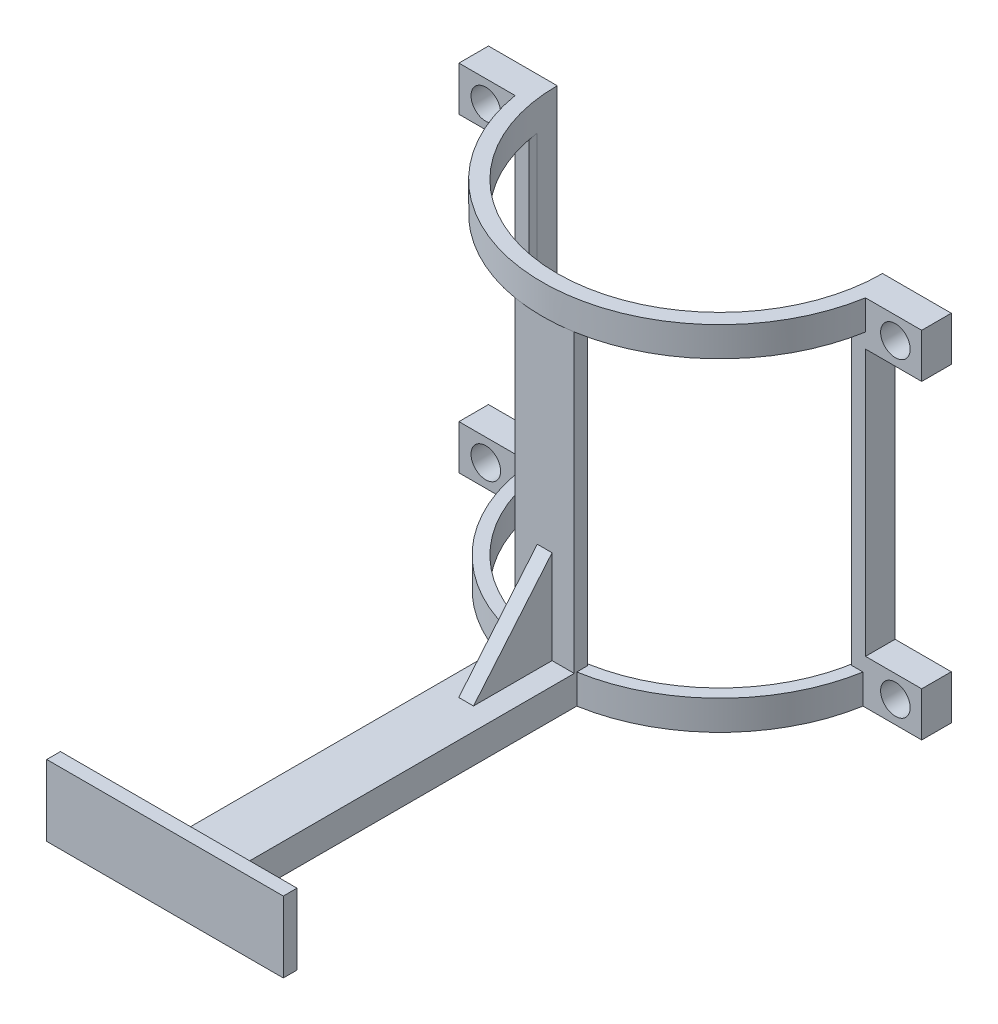
SolidWorks part; units mm, degrees
ref_plane "前视基准面" through (0, 0, 0) normal (0, 0, 1) x (1, 0, 0)
ref_plane "上视基准面" through (0, 0, 0) normal (0, 1, 0) x (1, 0, 0)
ref_plane "右视基准面" through (0, 0, 0) normal (1, 0, 0) x (0, 0, -1)
sketch "草图1" plane through (0, 0, 0) normal (0, 1, 0) x (1, 0, 0)
  line L0 (-118.5, 0) -> (-108.5, 0)
  line L1 (108.5, 0) -> (118.5, 0)
  arc A1 (-118.5, 0) -> (118.5, 0) centre (0, 0) ccw
  arc A2 (-108.5, 0) -> (108.5, 0) centre (0, 0) ccw
extrude "凸台-拉伸1" add sketch "草图1" along normal blind 20
ref_plane "基准面1" through (0, 0, 366) normal (0, 0, 1) x (1, 0, 0)
sketch "草图3" plane through (0, 0, 366) normal (0, 0, 1) x (1, 0, 0)
  line L0 (0, 0) -> (20, 0)
  line L2 (-118.5, 0) -> (118.5, 0) construction
  line L4 (20, 0) -> (20, 20)
  line L5 (118.5, 20) -> (-118.5, 20) construction
  line L6 (20, 20) -> (-20, 20)
  line L7 (-20, 20) -> (-20, 0)
  line L8 (-20, 0) -> (0, 0)
extrude "凸台-拉伸2" add sketch "草图3" against normal up to next
sketch "草图4" plane through (0, 20, 0) normal (0, 1, 0) x (1, 0, 0)
  line L1 (-20, -118.5) -> (20, -118.5)
  line L4 (-20, -116.8) -> (-20, -366) construction
  line L5 (20, -116.8) -> (20, -366) construction
  line L6 (20, -118.5) -> (20, -109.5)
  line L7 (20, -109.5) -> (-20, -109.5)
  line L8 (-20, -109.5) -> (-20, -118.5)
extrude "凸台-拉伸3" add sketch "草图4" along normal blind 200
sketch "草图5" plane through (0, 220, 0) normal (0, 1, 0) x (1, 0, 0)
  line L2 (118.5, 0) -> (108.5, 0) construction
  line L3 (-120.1759, 0) -> (-108.5, 0)
  line L4 (108.5, 0) -> (120.1759, 0)
  arc A0 (-108.5, 0) -> (108.5, 0) centre (0, 0) ccw
  arc A1 (120.1759, 0) -> (-120.1759, 0) centre (0, 0) cw
extrude "凸台-拉伸5" add sketch "草图5" along normal blind 20
sketch "草图10" plane through (0, 0, 0) normal (1, 0, 0) x (0, 0, -1)
  line L0 (-118.5, 83.1886) -> (-171.6421, 20)
  line L1 (-118.5, 220) -> (-118.5, 20) construction
  line L2 (-118.5, 20) -> (-366, 20) construction
rib "筋6" sketch "草图10" sketch "草图10" thickness 10 extrusion direction parallel to sketch draft on no parameters "D1"=10
sketch "草图11" plane through (0, 0, 366) normal (0, 0, 1) x (1, 0, 0)
  line L0 (-80, 48) -> (80, 48)
  line L2 (118.5, 20) -> (20, 20) construction
  line L3 (80, 38) -> (80, 20)
  line L4 (-20, 20) -> (-118.5, 20) construction
  line L5 (-80, 20) -> (-80, 0)
  line L6 (-118.5, 0) -> (-20, 0) construction
  line L7 (-80, 0) -> (80, 0)
  line L8 (20, 0) -> (118.5, 0) construction
  line L9 (80, 0) -> (80, 20)
  line L11 (-80, 38) -> (-80, 20)
  line L13 (80, 48) -> (80, 38)
  line L14 (-80, 48) -> (-80, 38)
extrude "凸台-拉伸6" add sketch "草图11" along normal blind 10
sketch "草图12" plane through (0, 0, 0) normal (0, 0, 1) x (1, 0, 0)
  line L0 (-109, 0) -> (-156.5, 0)
  line L1 (-156.5, 0) -> (-156.5, 30)
  line L2 (-156.5, 30) -> (-118.5, 30)
  line L3 (-109, 240) -> (-109, 0)
  line L4 (-109, 240) -> (-156.5, 240)
  line L5 (-156.5, 240) -> (-156.5, 210)
  line L6 (-118.5, 30) -> (-118.5, 210)
  line L7 (-118.5, 210) -> (-156.5, 210)
  line L8 (156.5, 0) -> (109, 0)
  line L10 (156.5, 0) -> (156.5, 30)
  line L11 (156.5, 30) -> (118.5, 30)
  line L12 (118.5, 30) -> (118.5, 210)
  line L13 (118.5, 210) -> (156.5, 210)
  line L14 (156.5, 210) -> (156.5, 240)
  line L15 (156.5, 240) -> (109, 240)
  line L17 (109, 240) -> (109, 0)
extrude "凸台-拉伸7" add sketch "草图12" along normal blind 20
sketch "草图13" plane through (0, 0, 0) normal (0, 0, -1) x (-1, 0, 0)
  line L0 (118.5, 30) -> (156.5, 30) construction
  line L1 (-156.5, 30) -> (-118.5, 30) construction
  line L2 (-118.5, 210) -> (-156.5, 210) construction
  line L3 (156.5, 210) -> (118.5, 210) construction
  circle A0 centre (138.3061, 225) radius 10
  circle A1 centre (138.3061, 15) radius 10
  circle A2 centre (-138.7046, 225) radius 10
  circle A3 centre (-138.7046, 15) radius 10
  dimension "D1" = 15
  dimension "D2" = 15
  dimension "D3" = 15
  dimension "D4" = 15
extrude "切除-拉伸1" cut sketch "草图13" against normal blind 20
sketch "草图14" plane through (0, 0, 0) normal (0, 1, 0) x (1, 0, 0)
  line L0 (-108.5, 0) -> (-156.5, 0) construction
  line L1 (156.5, 0) -> (108.5, 0) construction
  line L2 (-110, 0) -> (110, 0)
  arc A0 (-110, 0) -> (110, 0) centre (0, 0) ccw
extrude "切除-拉伸2" cut sketch "草图14" along normal blind 240
sketch "草图15" plane through (0, 48, 0) normal (0, 1, 0) x (1, 0, 0)
  line L0 (80, -375.2744) -> (-80, -375.2744)
  line L1 (80, -376) -> (80, -366) construction
  line L2 (-80, -376) -> (-80, -366) construction
  line L3 (-80, -375.2744) -> (-80, -376)
  line L4 (-80, -376) -> (80, -376)
  line L5 (80, -376) -> (80, -375.2744)
extrude "切除-拉伸3" cut sketch "草图15" against normal up to next
